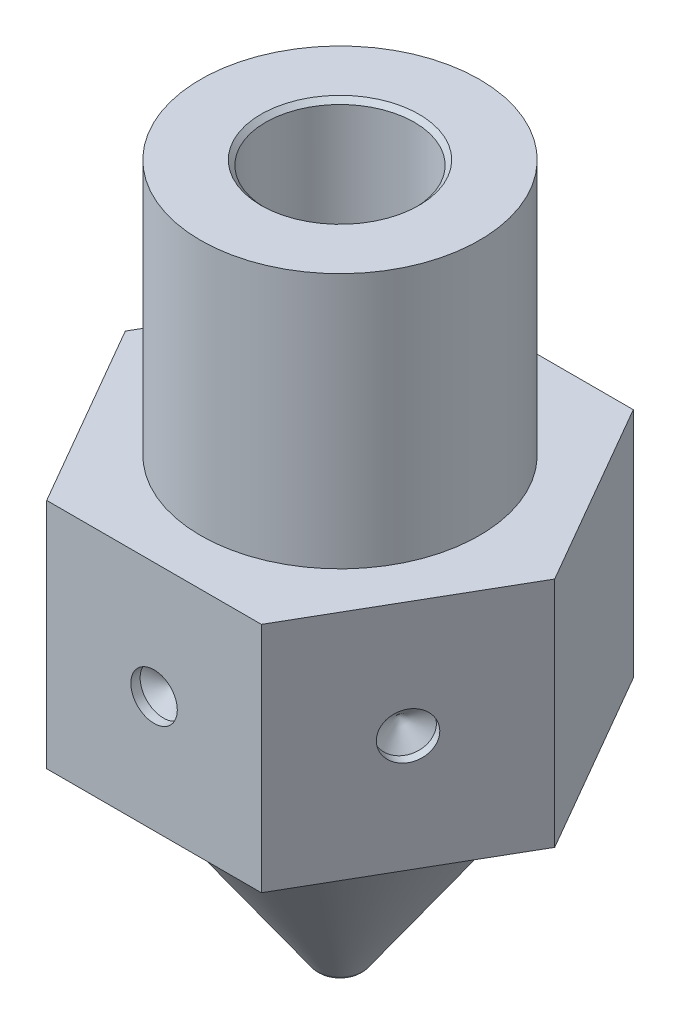
SolidWorks part; units mm, degrees
material "Latón"
ref_plane "Alzado" through (0, 0, 0) normal (0, 0, 1) x (1, 0, 0)
ref_plane "Planta" through (0, 0, 0) normal (0, 1, 0) x (1, 0, 0)
ref_plane "Vista lateral" through (0, 0, 0) normal (1, 0, 0) x (0, 0, -1)
sketch "Croquis1" plane through (0, 0, 0) normal (0, 0, 1) x (1, 0, 0)
  line L0 (0.2, 0) -> (0.25, 0)
  line L1 (0.4957, 0.1279) -> (3.5571, 4.5)
  line L2 (0.2, 0.8) -> (1.6, 2.7994)
  line L3 (7.0581, 9.5) -> (3, 9.5)
  line L4 (3, 9.5) -> (3, 15)
  line L5 (3, 15) -> (1.6, 15)
  line L6 (1.6, 15) -> (1.6, 2.7994)
  line L7 (0.2, 0.8) -> (0.2, 0)
  line L8 (0, 0) -> (0, 18.2336) construction
  line L11 (3.5571, 4.5) -> (5.706, 4.5)
  line L12 (5.706, 7.569) -> (5.706, 4.5)
  line L13 (5.706, 7.569) -> (7.0581, 9.5)
  arc A0 (0.25, 0) -> (0.4957, 0.1279) centre (0.25, 0.3) ccw
  point P14 (0.4062, 0)
  dimension "D8" = 0.05
  dimension "D10" = 0.3
  dimension "D1" = 0.2
  dimension "D3" = 1.6
  dimension "D4" = 3
  dimension "D5" = 15
  dimension "D6" = 5.5
  dimension "D7" = 35
  dimension "D9" = 0.8
  dimension "D13" = 4.5
revolve "Revolución1" add sketch "Croquis1" angle 360 about L8
cosmetic thread "Rosca cosmética1" parameters "D2"=4.891
sketch "Croquis2" plane through (0, 9.5, 0) normal (0, 1, 0) x (1, 0, 0)
  line L1 (2.3094, 4) -> (-2.3094, 4)
  line L2 (-2.3094, 4) -> (-4.6188, 0)
  line L3 (-4.6188, 0) -> (-2.3094, -4)
  line L4 (-2.3094, -4) -> (2.3094, -4)
  line L5 (2.3094, -4) -> (4.6188, 0)
  line L6 (4.6188, 0) -> (2.3094, 4)
  circle A0 centre (0, 0) radius 4 construction
  circle A2 centre (0, 0) radius 7.0581 construction
  circle A3 centre (0, 0) radius 7.0581
  dimension "D1" = 8
extrude "Cortar-Extruir1" cut sketch "Croquis2" against normal blind 7 from offset 1
chamfer "Chaflán1" distance 0.1 angle 45 1 edges at (0, 15, -1.6)
ref_plane "Plano1" through (4.6188, 4.5, 0) normal (0, 1, 0) x (1, 0, 0)
sketch "Croquis3" plane through (0, 0, 4) normal (0, 0, 1) x (1, 0, 0)
  line L0 (-2.3094, 9.5) -> (2.3094, 4.5) construction
  point P4 (0, 7)
sketch "Croquis4" plane through (3.4641, 0, 2) normal (0.866, 0, 0.5) x (0.5, 0, -0.866)
  line L0 (-2.3094, 9.5) -> (2.3094, 4.5) construction
  point P4 (0, 7)
hole_wizard "Diámetro de taladro Ø1.0 (1)1" positions "Croquis3D1" profile "Croquis5" hole size "Ø1.0" standard "Din"
sketch3d "Croquis3D1"
  point P0 (3.4641, 7, 2)
  point P3 (0, 7, 4)
sketch "Croquis5" plane through (3.4641, 7, 2) normal (0, 1, 0) x (0.5, 0, -0.866)
  line L0 (0, 0) -> (0, 0.5004)
  line L1 (0, 0.5004) -> (0.5, 0.2)
  line L2 (0.5, 0.2) -> (0.5, 0)
  line L5 (0.5, 0) -> (0, 0)
  line L10 (0, 0.5004) -> (-0.5, 0.2) construction
  line L11 (0, -6.35) -> (0, 107.95) construction
  dimension "Diámetro de taladro" = 1
  dimension "Profundidad de taladro" = 0.2
  dimension "Ángulo de perforador" = 118
